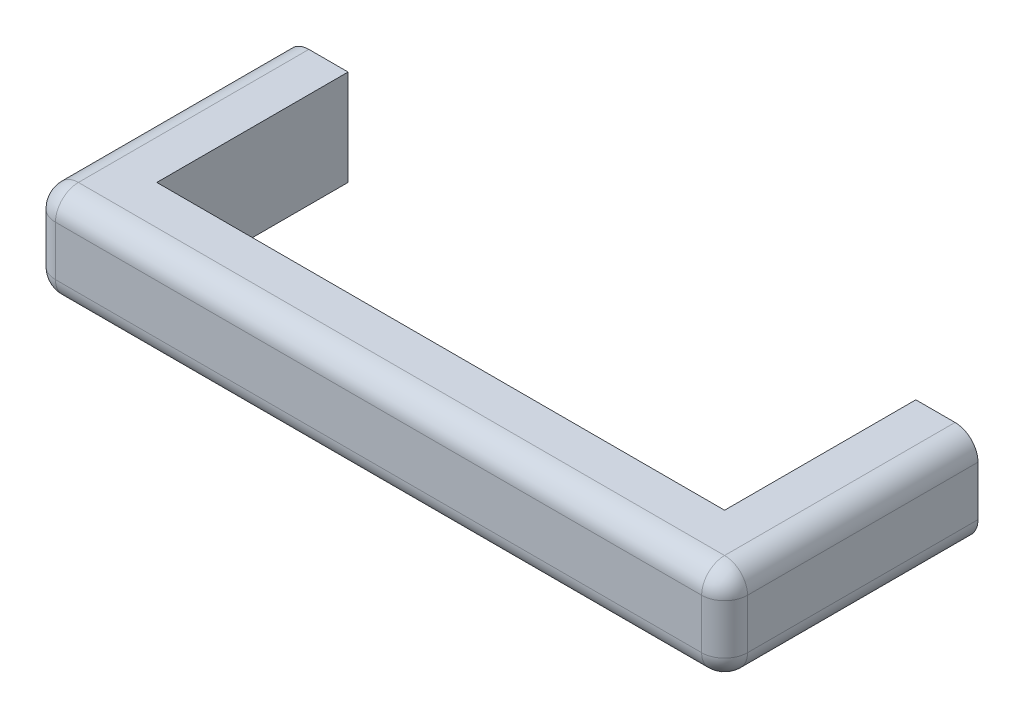
SolidWorks part; units mm, degrees
ref_plane "Front Plane" through (0, 0, 0) normal (0, 0, 1) x (1, 0, 0)
ref_plane "Top Plane" through (0, 0, 0) normal (0, 1, 0) x (1, 0, 0)
ref_plane "Right Plane" through (0, 0, 0) normal (1, 0, 0) x (0, 0, -1)
sketch "Sketch1" plane through (0, 0, 0) normal (0, 1, 0) x (1, 0, 0)
  line L0 (377, 0) -> (-377, 0)
  line L1 (-377, 0) -> (-377, 254)
  line L2 (-377, 254) -> (-459.55, 254)
  line L3 (-459.55, 254) -> (-459.55, -82.55)
  line L4 (-459.55, -82.55) -> (459.55, -82.55)
  line L5 (459.55, -82.55) -> (459.55, 254)
  line L6 (459.55, 254) -> (377, 254)
  line L7 (377, 254) -> (377, 0)
  point P4 (0, 0)
  dimension "D1" = 254
  dimension "D2" = 82.55
  dimension "D3" = 82.55
  dimension "D4" = 754
extrude "Boss-Extrude1" add sketch "Sketch1" along normal blind 61.9125 and the other way blind 65.0875
fillet "Fillet1" radius 30.48 8 edges at (-459.55, -1.5875, 82.55) (459.55, -1.5875, 82.55) (459.55, -65.0875, -85.725) (459.55, 61.9125, -85.725) (-459.55, -65.0875, -85.725) (0, -65.0875, 82.55) (-459.55, 61.9125, -85.725) (0, 61.9125, 82.55)
